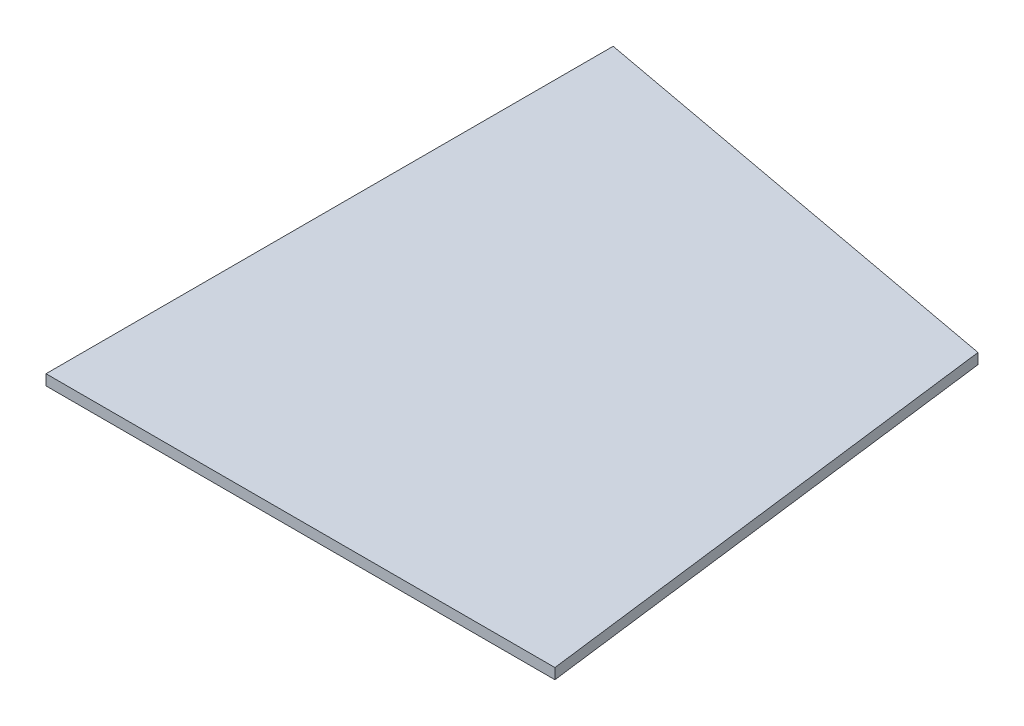
SolidWorks part; units mm, degrees
ref_plane "Front Plane" through (0, 0, 0) normal (0, 0, 1) x (1, 0, 0)
ref_plane "Top Plane" through (0, 0, 0) normal (0, 1, 0) x (1, 0, 0)
ref_plane "Right Plane" through (0, 0, 0) normal (1, 0, 0) x (0, 0, -1)
sketch "Sketch2" plane through (0, 0, 0) normal (0, 1, 0) x (1, 0, 0)
  line L0 (0, 0) -> (0, 293.6875)
  line L1 (0, 0) -> (263.525, 0)
  line L2 (0, 293.6875) -> (231.775, 250.825)
  line L3 (231.775, 250.825) -> (263.525, 0)
  dimension "D1" = 263.525
  dimension "D2" = 293.6875
  dimension "D3" = 231.775
  dimension "D4" = 250.825
extrude "Boss-Extrude1" add sketch "Sketch2" along normal blind 5.4737 contours L2 L3 L1 L0
